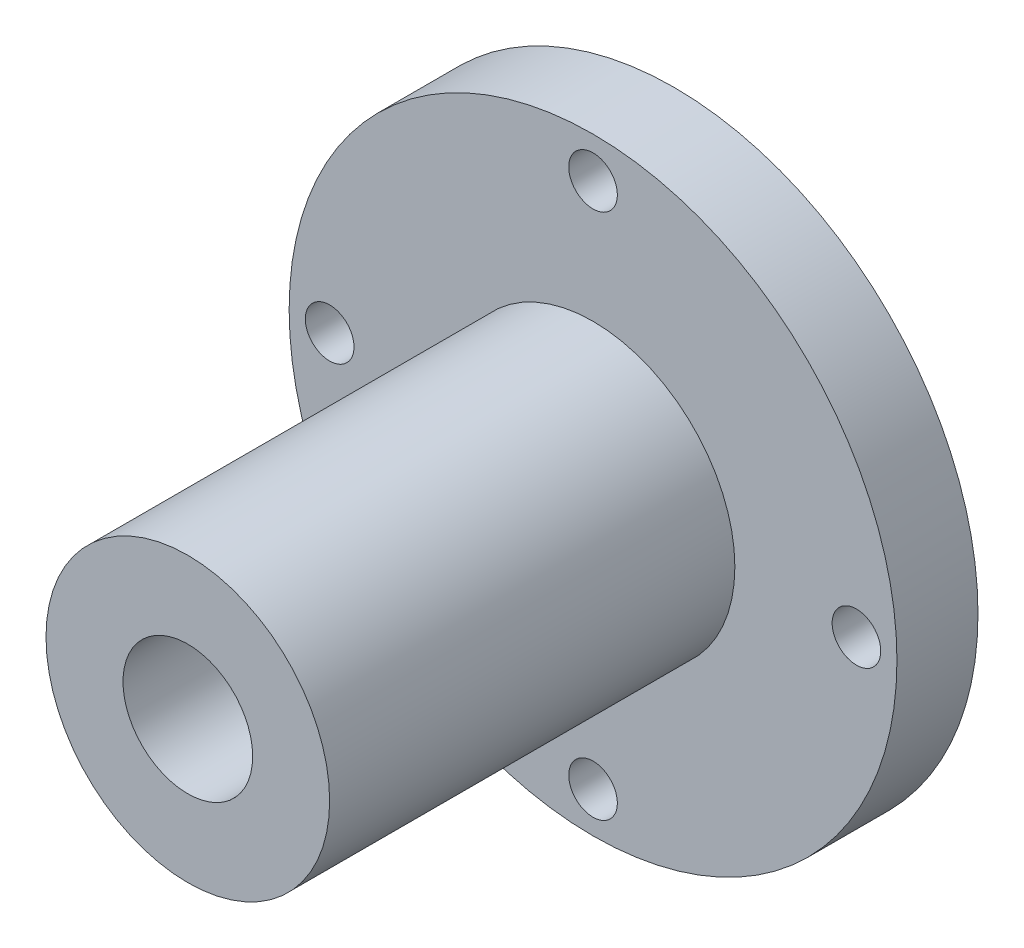
SolidWorks part; units mm, degrees
ref_plane "前视基准面" through (0, 0, 0) normal (0, 0, 1) x (1, 0, 0)
ref_plane "上视基准面" through (0, 0, 0) normal (0, 1, 0) x (1, 0, 0)
ref_plane "右视基准面" through (0, 0, 0) normal (1, 0, 0) x (0, 0, -1)
sketch "草图1" plane through (0, 0, 0) normal (0, 0, 1) x (1, 0, 0)
  circle A0 centre (0, 0) radius 37.5
  dimension "D1" = 75
extrude "凸台-拉伸1" add sketch "草图1" along normal blind 10
sketch "草图2" plane through (0, 0, 10) normal (0, 0, 1) x (1, 0, 0)
  circle A0 centre (0, 0) radius 17.5
  dimension "D1" = 35
extrude "凸台-拉伸2" add sketch "草图2" along normal blind 50
sketch "草图3" plane through (0, 0, 60) normal (0, 0, 1) x (1, 0, 0)
  circle A0 centre (0, 0) radius 8
  dimension "D1" = 16
extrude "切除-拉伸1" cut sketch "草图3" against normal through all
sketch "草图4" plane through (0, 0, 10) normal (0, 0, 1) x (1, 0, 0)
  circle A0 centre (0, 32.5) radius 3
  circle A1 centre (32.5, 0) radius 3
  circle A2 centre (0, -32.5) radius 3
  circle A3 centre (-32.5, 0) radius 3
  point P12 (0, 0)
  dimension "D1" = 6
  dimension "D2" = 32.5
  dimension "D3" = 4
extrude "切除-拉伸2" cut sketch "草图4" against normal blind 10
